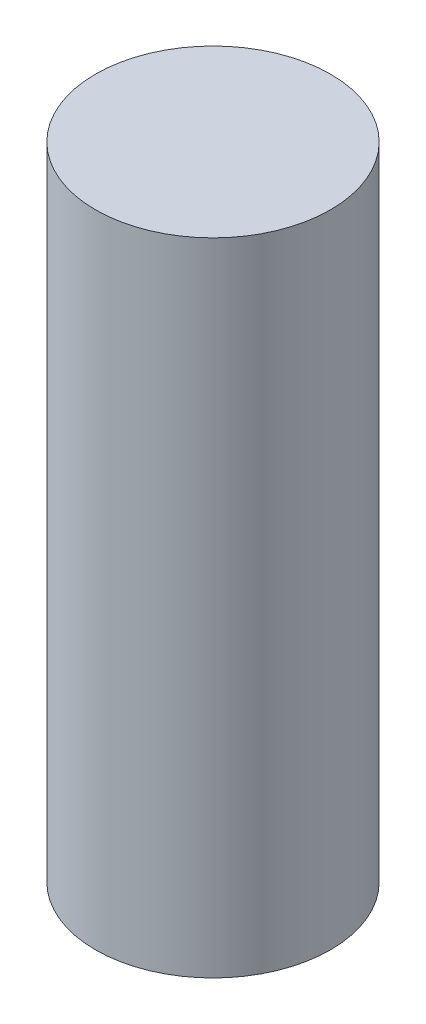
SolidWorks part; units mm, degrees
ref_plane "Front Plane" through (0, 0, 0) normal (0, 0, 1) x (1, 0, 0)
ref_plane "Top Plane" through (0, 0, 0) normal (0, 1, 0) x (1, 0, 0)
ref_plane "Right Plane" through (0, 0, 0) normal (1, 0, 0) x (0, 0, -1)
sketch "Sketch1" plane through (0, 0, 0) normal (0, 1, 0) x (1, 0, 0)
  circle A0 centre (0, 0) radius 2.75
  dimension "D1" = 5.5
extrude "Boss-Extrude1" add sketch "Sketch1" along normal blind 15
